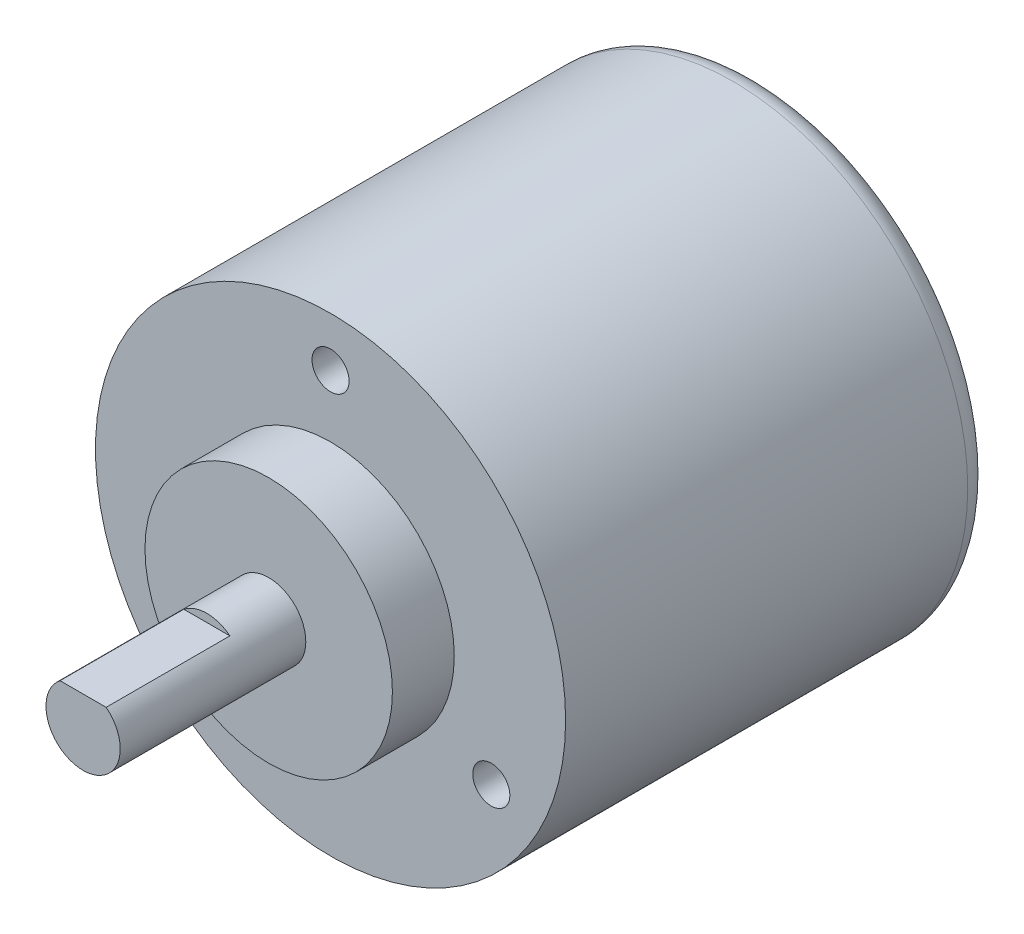
SolidWorks part; units mm, degrees
ref_plane "Ön Düzlem" through (0, 0, 0) normal (0, 0, 1) x (1, 0, 0)
ref_plane "Üst Düzlem" through (0, 0, 0) normal (0, 1, 0) x (1, 0, 0)
ref_plane "Sağ Düzlem" through (0, 0, 0) normal (1, 0, 0) x (0, 0, -1)
sketch "Sketch1" plane through (0, 0, 0) normal (0, 0, 1) x (1, 0, 0)
  circle A0 centre (0, 0) radius 19
  dimension "D1" = 38
extrude "Boss-Extrude1" add sketch "Sketch1" along normal blind 34.5
sketch "Sketch2" plane through (0, 0, 34.5) normal (0, 0, 1) x (1, 0, 0)
  circle A0 centre (0, 0) radius 10
  dimension "D1" = 20
extrude "Boss-Extrude2" add sketch "Sketch2" along normal blind 5
sketch "Sketch3" plane through (0, 0, 39.5) normal (0, 0, 1) x (1, 0, 0)
  circle A0 centre (0, 0) radius 3
  dimension "D1" = 6
extrude "Boss-Extrude3" add sketch "Sketch3" along normal blind 15
sketch "Sketch4" plane through (0, 0, 0) normal (1, 0, 0) x (0, 0, -1)
  line L0 (-54.5, 3) -> (-54.5, 2.35)
  line L1 (-54.5, 3) -> (-54.5, -3) construction
  line L2 (-54.5, 2.35) -> (-44.5, 2.35)
  line L3 (-44.5, 2.35) -> (-44.5, 3)
  line L4 (-39.5, 3) -> (-54.5, 3) construction
  line L5 (-44.5, 3) -> (-54.5, 3)
  line L6 (-54.5, -3) -> (-39.5, -3) construction
  dimension "D1" = 10
  dimension "D2" = 5.35
extrude "Cut-Extrude1" cut sketch "Sketch4" against normal through all both and the other way through all
fillet "Fillet1" radius 2 1 edges at (19, 0, 0)
sketch "Sketch5" plane through (0, 0, 34.5) normal (0, 0, 1) x (1, 0, 0)
  circle A0 centre (0, 0) radius 15 construction
  circle A1 centre (0, 15) radius 1.5
  circle A2 centre (12.9904, -7.5) radius 1.5
  circle A3 centre (-12.9904, -7.5) radius 1.5
  point P6 (0, 0)
  point P7 (10.2915, -2.8254)
  point P12 (0, 0)
  point P13 (0, 0)
  dimension "D1" = 30
  dimension "D2" = 3
  dimension "D3" = 3
extrude "Cut-Extrude2" cut sketch "Sketch5" against normal blind 3
